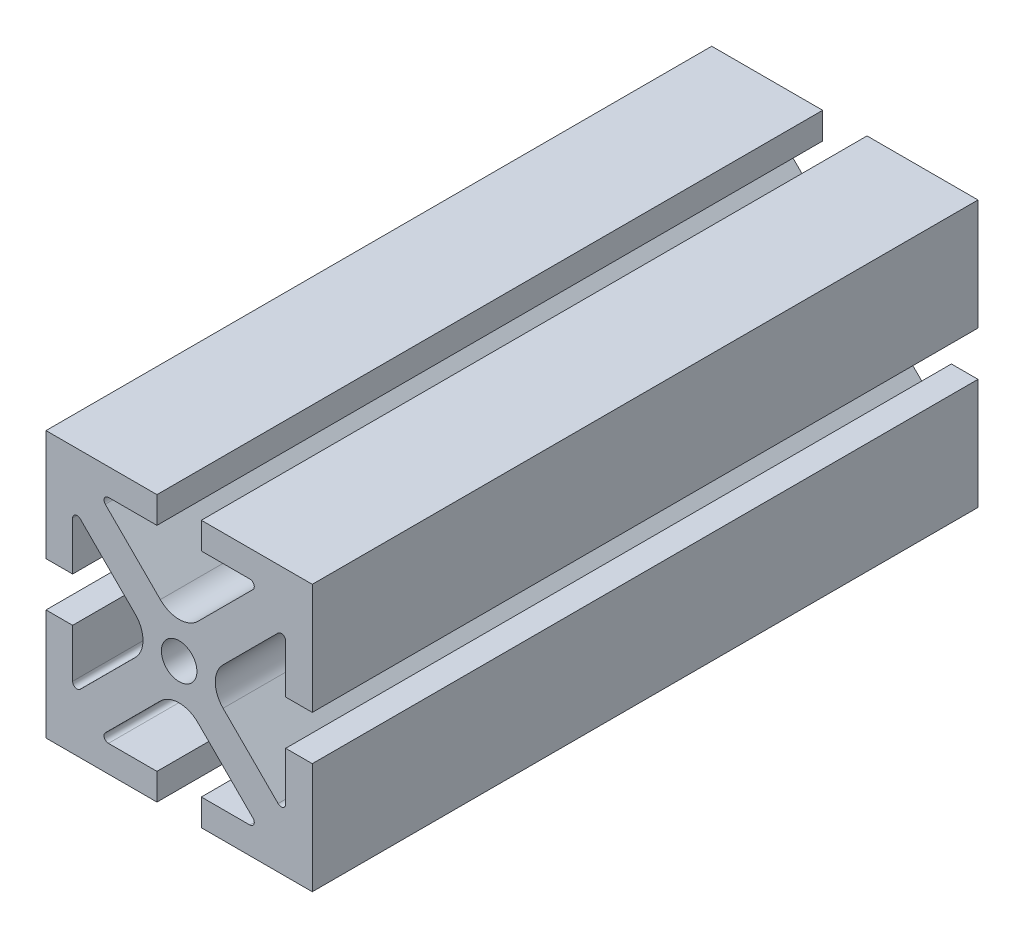
SolidWorks part; units mm, degrees
ref_plane "Front Plane" through (0, 0, 0) normal (0, 0, 1) x (1, 0, 0)
ref_plane "Top Plane" through (0, 0, 0) normal (0, 1, 0) x (1, 0, 0)
ref_plane "Right Plane" through (0, 0, 0) normal (1, 0, 0) x (0, 0, -1)
sketch "Sketch1" plane through (0, 0, 0) normal (0, 0, 1) x (1, 0, 0)
  line L0 (-5, 30) -> (-5, 24)
  line L1 (-30, -30) -> (-5, -30)
  line L2 (-30, -30) -> (-30, -5)
  line L3 (-30, 30) -> (-5, 30)
  line L4 (30, -30) -> (30, -5)
  line L5 (-30, -30) -> (30, 30) construction
  line L6 (-30, 30) -> (30, -30) construction
  line L7 (-5, 24) -> (-15.9289, 24)
  line L8 (-16.636, 22.2929) -> (-4.2426, 9.8995)
  line L9 (-30, 5) -> (-24, 5)
  line L10 (-24, 5) -> (-24, 15.9289)
  line L11 (-22.2929, 16.636) -> (-9.8995, 4.2426)
  line L12 (-40, 0) -> (40, 0) construction
  line L13 (0, -40) -> (0, 40) construction
  line L14 (-5, -30) -> (-5, -24)
  line L15 (-5, -24) -> (-15.9289, -24)
  line L16 (-16.636, -22.2929) -> (-4.2426, -9.8995)
  line L17 (-22.2929, -16.636) -> (-9.8995, -4.2426)
  line L18 (-30, -5) -> (-24, -5)
  line L19 (-24, -5) -> (-24, -15.9289)
  line L20 (5, 30) -> (5, 24)
  line L21 (5, 24) -> (15.9289, 24)
  line L22 (16.636, 22.2929) -> (4.2426, 9.8995)
  line L23 (22.2929, 16.636) -> (9.8995, 4.2426)
  line L24 (24, 5) -> (24, 15.9289)
  line L25 (30, 5) -> (24, 5)
  line L26 (30, -5) -> (24, -5)
  line L27 (24, -5) -> (24, -15.9289)
  line L28 (22.2929, -16.636) -> (9.8995, -4.2426)
  line L29 (16.636, -22.2929) -> (4.2426, -9.8995)
  line L30 (5, -30) -> (5, -24)
  line L31 (5, -24) -> (15.9289, -24)
  line L32 (5, 30) -> (30, 30)
  line L33 (30, 5) -> (30, 30)
  line L34 (5, -30) -> (30, -30)
  line L35 (-30, 5) -> (-30, 30)
  arc A0 (-4.2426, 9.8995) -> (4.2426, 9.8995) centre (0, 14.1421) ccw
  arc A1 (9.8995, 4.2426) -> (9.8995, -4.2426) centre (14.1421, 0) ccw
  arc A2 (4.2426, -9.8995) -> (-4.2426, -9.8995) centre (0, -14.1421) ccw
  arc A3 (-9.8995, -4.2426) -> (-9.8995, 4.2426) centre (-14.1421, 0) ccw
  arc A4 (-15.9289, -24) -> (-16.636, -22.2929) centre (-15.9289, -23) cw
  arc A5 (-22.2929, -16.636) -> (-24, -15.9289) centre (-23, -15.9289) cw
  arc A6 (-22.2929, 16.636) -> (-24, 15.9289) centre (-23, 15.9289) ccw
  arc A7 (-15.9289, 24) -> (-16.636, 22.2929) centre (-15.9289, 23) ccw
  arc A8 (16.636, 22.2929) -> (15.9289, 24) centre (15.9289, 23) ccw
  arc A9 (24, 15.9289) -> (22.2929, 16.636) centre (23, 15.9289) ccw
  arc A10 (24, -15.9289) -> (22.2929, -16.636) centre (23, -15.9289) cw
  arc A11 (16.636, -22.2929) -> (15.9289, -24) centre (15.9289, -23) cw
  point P0 (0, 0)
  point P40 (0, 5.6569)
  point P43 (5.6569, 0)
  point P46 (0, -5.6569)
  point P49 (-5.6569, 0)
  point P52 (-18.3431, -24)
  point P55 (-24, -18.3431)
  point P58 (-24, 18.3431)
  point P61 (-18.3431, 24)
  point P64 (18.3431, 24)
  point P67 (24, 18.3431)
  point P70 (24, -18.3431)
  point P73 (18.3431, -24)
  dimension "D5" = 6
  dimension "D7" = 1
  dimension "D1" = 60
  dimension "D2" = 6
  dimension "D3" = 4
  dimension "D4" = 25
extrude "Boss-Extrude1" add sketch "Sketch1" along normal blind 150 contours L35 L3 L0 L7 A7 L8 A0 L22 A8 L21 L20 L32 L33 L25 L24 A9 L23 A1 L28 A10 L27 L26 L4 L34 L30 L31 A11 L29 A2 L16 A4 L15 L14 L1 L2 L18 L19 A5 L17 A3 L11 A6 L10 L9
ref_plane "Plane1" through (0, 0, 75) normal (0, 0, 1) x (1, 0, 0)
sketch "Sketch2" plane through (0, 0, 0) normal (0, 0, -1) x (-1, 0, 0)
  circle A0 centre (0, 0) radius 3.75
  dimension "D1" = 7.5
extrude "Cut-Extrude1" cut sketch "Sketch2" against normal through all
sketch "Sketch3" plane through (-30, 0, 0) normal (-1, 0, 0) x (0, 0, 1)
  line L0 (75, -16.5) -> (75, 16.5) construction
  circle A0 centre (75, 0) radius 4
  circle A1 centre (30, 0) radius 4
  dimension "D1" = 8
  dimension "D2" = 8
  dimension "D3" = 30
extrude "Cut-Extrude2" cut sketch "Sketch3" against normal through all
sketch "Sketch5" plane through (0, 0, 0) normal (0, 0, -1) x (-1, 0, 0)
  circle A0 centre (0, 0) radius 4
  dimension "D1" = 8
extrude "Cut-Extrude5" cut sketch "Sketch5" against normal blind 20
sketch "Sketch6" plane through (0, 0, 150) normal (0, 0, 1) x (1, 0, 0)
  circle A0 centre (0, 0) radius 4
  dimension "D1" = 8
extrude "Cut-Extrude6" cut sketch "Sketch6" against normal blind 20
scale "Scale1" scale about centroid uniform scaling yes scale factor 0.5
